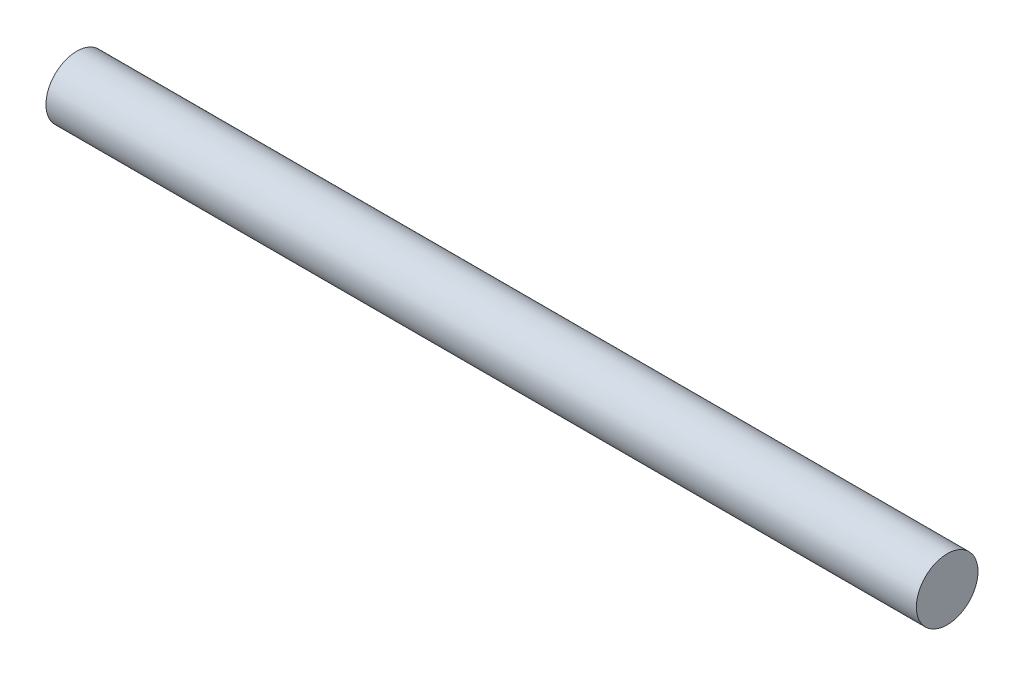
SolidWorks part; units mm, degrees
ref_plane "Front Plane" through (0, 0, 0) normal (0, 0, 1) x (1, 0, 0)
ref_plane "Top Plane" through (0, 0, 0) normal (0, 1, 0) x (1, 0, 0)
ref_plane "Right Plane" through (0, 0, 0) normal (1, 0, 0) x (0, 0, -1)
sketch "Sketch1" plane through (0, 0, 0) normal (1, 0, 0) x (0, 0, -1)
  circle A0 centre (0, 0) radius 25.365
  dimension "D1" = 50.73
extrude "Boss-Extrude1" add sketch "Sketch1" along normal blind 716.28
